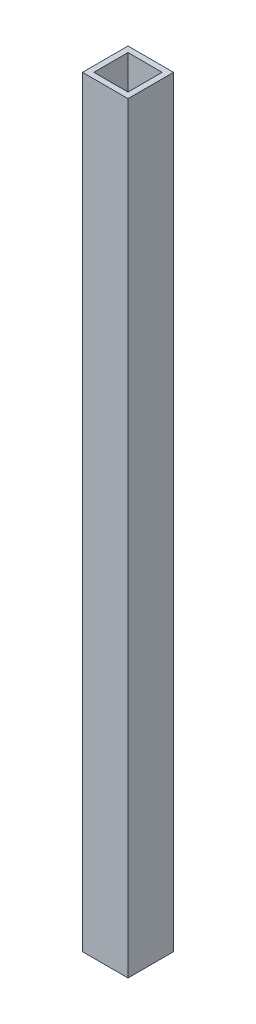
SolidWorks part; units mm, degrees
material "1060 Alloy"
ref_plane "Front Plane" through (0, 0, 0) normal (0, 0, 1) x (1, 0, 0)
ref_plane "Top Plane" through (0, 0, 0) normal (0, 1, 0) x (1, 0, 0)
ref_plane "Right Plane" through (0, 0, 0) normal (1, 0, 0) x (0, 0, -1)
sketch "Sketch1" plane through (0, 0, 0) normal (0, 1, 0) x (1, 0, 0)
  line L0 (-9.525, -9.525) -> (-9.525, 9.525)
  line L1 (-12.7, -12.7) -> (12.7, -12.7)
  line L2 (-12.7, -12.7) -> (-12.7, 12.7)
  line L3 (-12.7, 12.7) -> (12.7, 12.7)
  line L4 (12.7, -12.7) -> (12.7, 12.7)
  line L5 (-12.7, -12.7) -> (12.7, 12.7) construction
  line L6 (-12.7, 12.7) -> (12.7, -12.7) construction
  line L7 (-9.525, 9.525) -> (9.525, 9.525)
  line L8 (9.525, -9.525) -> (9.525, 9.525)
  line L9 (-9.525, -9.525) -> (9.525, -9.525)
  point P0 (0, 0)
  dimension "D1" = 25.4
  dimension "D2" = 25.4
  dimension "D3" = 3.175
extrude "Boss-Extrude1" add sketch "Sketch1" along normal blind 424.434 contours L1 L4 L3 L2 L9 L0 L7 L8
